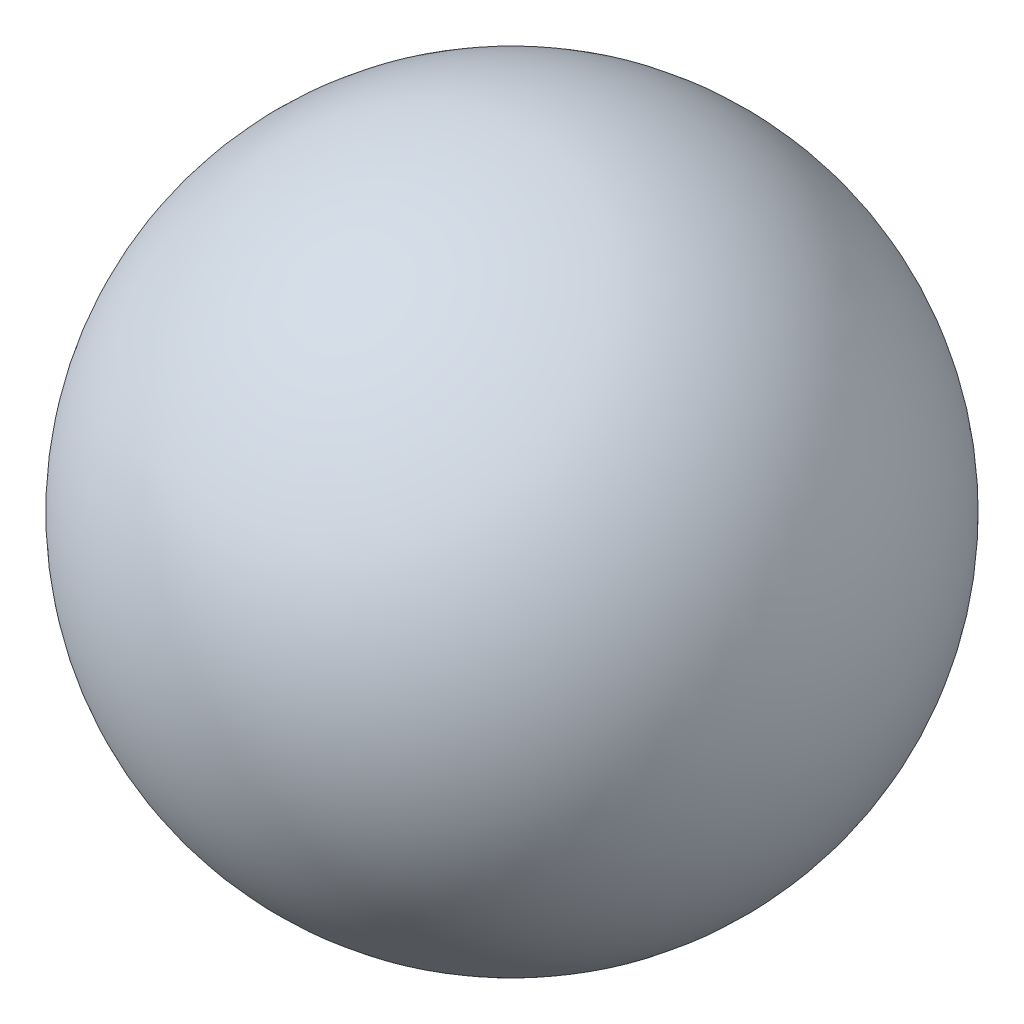
SolidWorks part; units mm, degrees
ref_plane "前视基准面" through (0, 0, 0) normal (0, 0, 1) x (1, 0, 0)
ref_plane "上视基准面" through (0, 0, 0) normal (0, 1, 0) x (1, 0, 0)
ref_plane "右视基准面" through (0, 0, 0) normal (1, 0, 0) x (0, 0, -1)
sketch "草图1" plane through (0, 0, 0) normal (0, 0, 1) x (1, 0, 0)
  line L0 (0, -2.8782) -> (0, 3.4707) construction
  circle A0 centre (0, 0) radius 2.5
  dimension "D1" = 5
revolve "旋转5" add sketch "草图1" angle 360 about L0
